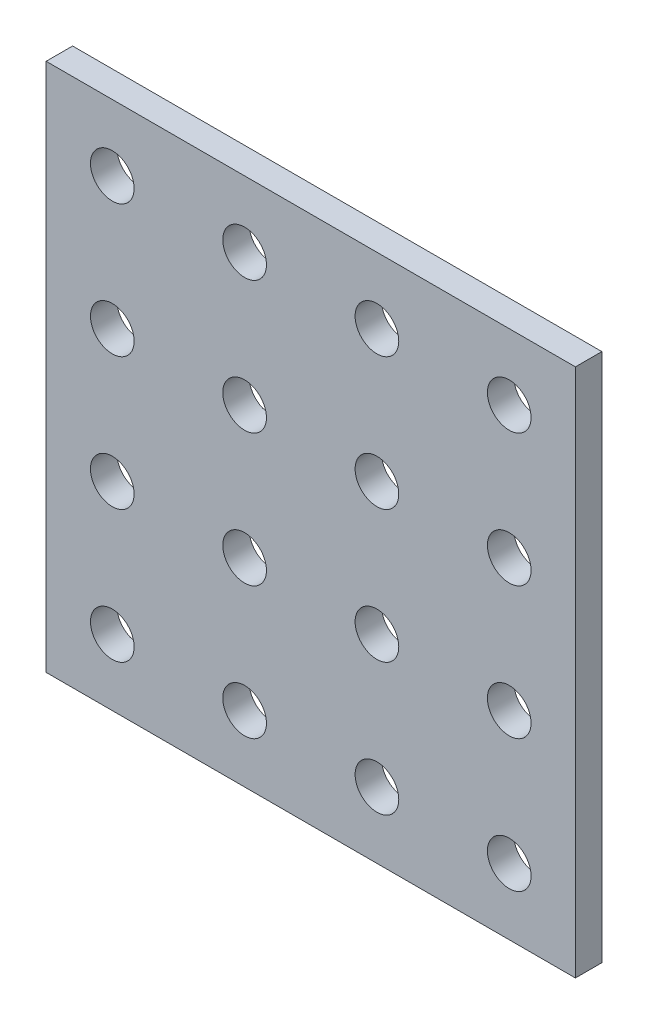
SolidWorks part; units mm, degrees
ref_plane "Front Plane" through (0, 0, 0) normal (0, 0, 1) x (1, 0, 0)
ref_plane "Top Plane" through (0, 0, 0) normal (0, 1, 0) x (1, 0, 0)
ref_plane "Right Plane" through (0, 0, 0) normal (1, 0, 0) x (0, 0, -1)
sketch "Sketch1" plane through (0, 0, 0) normal (0, 0, 1) x (1, 0, 0)
  line L1 (-20, -20) -> (20, -20)
  line L2 (-20, -20) -> (-20, 20)
  line L3 (-20, 20) -> (20, 20)
  line L4 (20, -20) -> (20, 20)
  line L5 (-20, -20) -> (20, 20) construction
  line L6 (-20, 20) -> (20, -20) construction
  point P0 (0, 0)
  dimension "D1" = 40
  dimension "D2" = 40
extrude "Boss-Extrude1" add sketch "Sketch1" along normal blind 2
sketch "Sketch2" plane through (0, 0, 2) normal (0, 0, 1) x (1, 0, 0)
  line L0 (-20, 20) -> (-20, -20) construction
  line L2 (20, 20) -> (-20, 20) construction
  circle A0 centre (-15, 15) radius 1.65
  dimension "D1" = 3.3
  dimension "D2" = 5
  dimension "D3" = 5
extrude "Cut-Extrude1" cut sketch "Sketch2" against normal through all
pattern_linear "LPattern1" count 4 spacing 10 along (0, -1, 0) count 4 spacing 10 along (1, 0, 0) of "Cut-Extrude1"
